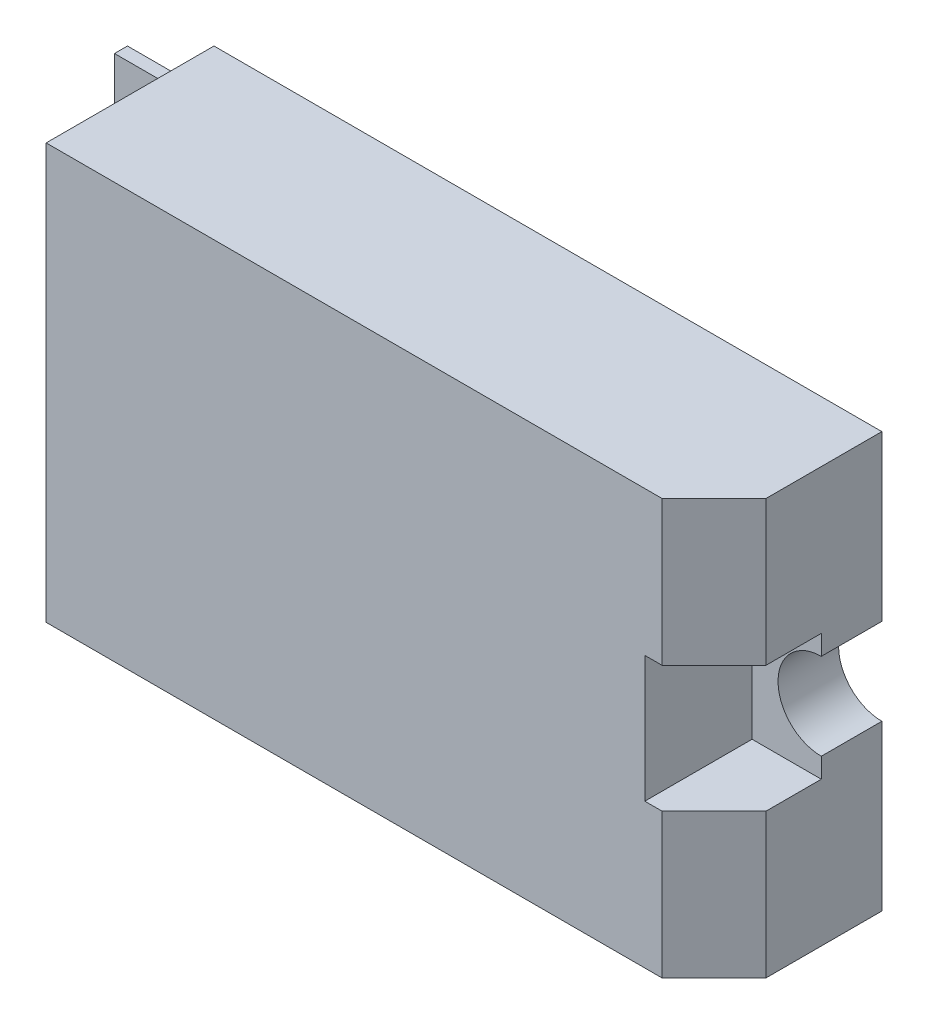
SolidWorks part; units mm, degrees
ref_plane "前视基准面" through (0, 0, 0) normal (0, 0, 1) x (1, 0, 0)
ref_plane "上视基准面" through (0, 0, 0) normal (0, 1, 0) x (1, 0, 0)
ref_plane "右视基准面" through (0, 0, 0) normal (1, 0, 0) x (0, 0, -1)
other "Configuration Table"
sketch "草图1" plane through (28.6936, -23.9963, -44.1125) normal (0, 0, 1) x (1, 0, 0)
  line L1 (-65.7922, -21.8632) -> (-27.1922, -21.8632)
  line L2 (-65.7922, -21.8632) -> (-65.7922, -45.8632)
  line L3 (-65.7922, -45.8632) -> (-27.1922, -45.8632)
  line L4 (-27.1922, -21.8632) -> (-27.1922, -45.8632)
  dimension "D1" = 38.6
  dimension "D2" = 24
extrude "凸台-拉伸1" add sketch "草图1" along normal blind 9.7
sketch "草图2" plane through (-37.0986, 0, 0) normal (-1, 0, 0) x (0, 0, 1)
  line L0 (-44.1125, -45.8595) -> (-44.1125, -69.8595) construction
  line L1 (-43.1125, -47.3595) -> (-42.3625, -47.3595)
  line L2 (-43.1125, -47.3595) -> (-43.1125, -68.3595)
  line L3 (-43.1125, -68.3595) -> (-42.3625, -68.3595)
  line L4 (-42.3625, -47.3595) -> (-42.3625, -68.3595)
  line L6 (9.7, -57.8595) -> (16.5892, -57.8595) construction
  line L7 (-34.4125, -45.8595) -> (-34.4125, -69.8595) construction
  point P4 (-42.7375, -47.3595)
  point P7 (-42.3625, -57.8595)
  point P12 (-34.4125, -57.8595)
  dimension "D1" = 21
  dimension "D2" = 0.75
  dimension "D3" = 1
extrude "凸台-拉伸2" add sketch "草图2" along normal blind 4
chamfer "倒角1" distance 3 angle 45 1 edges at (1.5014, -57.8595, -34.4125)
sketch "草图3" plane through (0, 0, -34.4125) normal (0, 0, 1) x (1, 0, 0)
  line L0 (1.5014, -45.8595) -> (1.5014, -69.8595) construction
  line L1 (1.5014, -54.2095) -> (-2.4986, -54.2095)
  line L2 (1.5014, -54.2095) -> (1.5014, -61.5095)
  line L3 (1.5014, -61.5095) -> (-2.4986, -61.5095)
  line L4 (-2.4986, -54.2095) -> (-2.4986, -61.5095)
  line L5 (-37.0986, -45.8595) -> (-37.0986, -69.8595) construction
  point P8 (-37.0986, -57.8595)
  point P9 (-2.4986, -57.8595)
  dimension "D1" = 7.3
  dimension "D2" = 4
extrude "切除-拉伸1" cut sketch "草图3" against normal blind 6.2
sketch "草图4" plane through (0, 0, -40.6125) normal (0, 0, 1) x (1, 0, 0)
  line L0 (1.5014, -61.5095) -> (1.5014, -54.2095) construction
  circle A0 centre (1.5014, -57.8595) radius 2.5
  dimension "D1" = 5
extrude "切除-拉伸2" cut sketch "草图4" against normal through all
